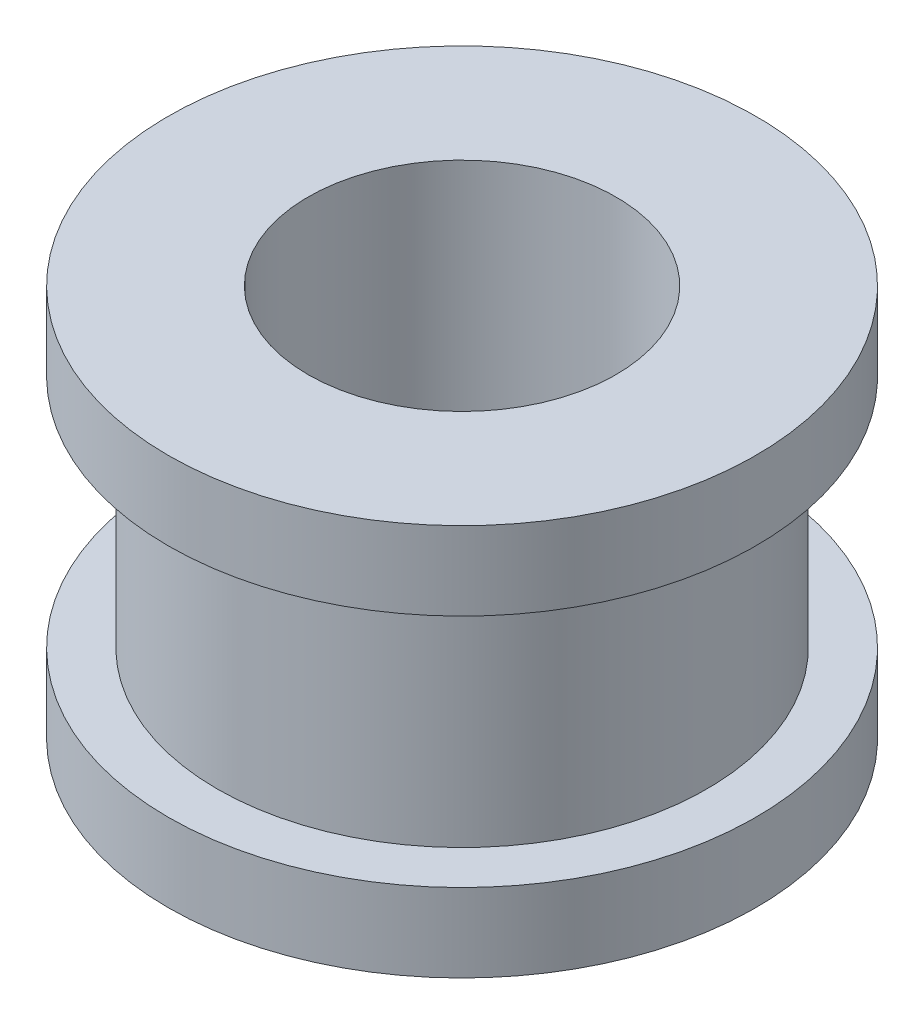
SolidWorks part; units mm, degrees
ref_plane "Front Plane" through (0, 0, 0) normal (0, 0, 1) x (1, 0, 0)
ref_plane "Top Plane" through (0, 0, 0) normal (0, 1, 0) x (1, 0, 0)
ref_plane "Right Plane" through (0, 0, 0) normal (1, 0, 0) x (0, 0, -1)
sketch "Sketch1" plane through (0, 0, 0) normal (0, 1, 0) x (1, 0, 0)
  circle A0 centre (0, 0) radius 2.4956
  circle A1 centre (0, 0) radius 4.7625
  dimension "D1" = 4.9911
  dimension "D2" = 9.525
extrude "Boss-Extrude1" add sketch "Sketch1" along normal blind 6.35
sketch "Sketch2" plane through (0, 6.35, 0) normal (0, 1, 0) x (1, 0, 0)
  circle A0 centre (0, 0) radius 4.7625
  circle A1 centre (0, 0) radius 4.7625 construction
  circle A2 centre (0, 0) radius 3.9688
  dimension "D1" = 0.7937
extrude "Cut-Extrude1" cut sketch "Sketch2" along normal offset from surface (3.81 mm away) 1.27 from offset 5.08
